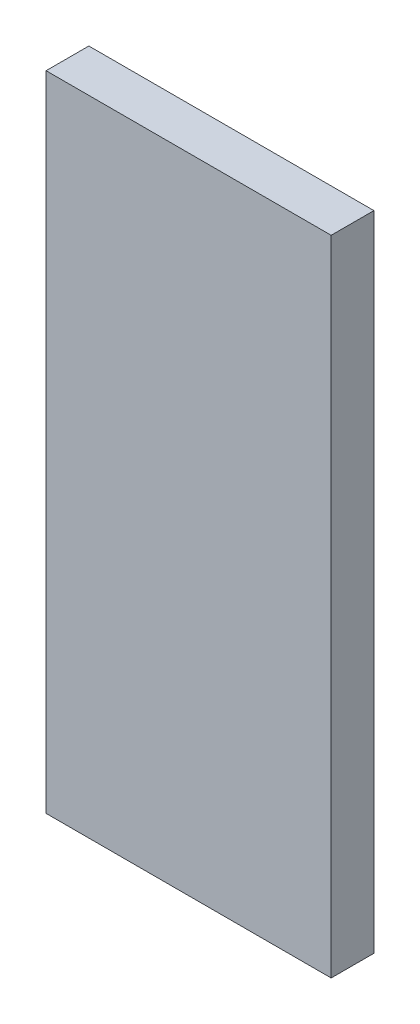
SolidWorks part; units mm, degrees
ref_plane "Alzado" through (0, 0, 0) normal (0, 0, 1) x (1, 0, 0)
ref_plane "Planta" through (0, 0, 0) normal (0, 1, 0) x (1, 0, 0)
ref_plane "Vista lateral" through (0, 0, 0) normal (1, 0, 0) x (0, 0, -1)
sketch "Croquis1" plane through (0, 0, 0) normal (0, 0, 1) x (1, 0, 0)
  line L1 (-40, -90.25) -> (40, -90.25)
  line L2 (-40, -90.25) -> (-40, 90.25)
  line L3 (-40, 90.25) -> (40, 90.25)
  line L4 (40, -90.25) -> (40, 90.25)
  line L5 (-40, -90.25) -> (40, 90.25) construction
  line L6 (-40, 90.25) -> (40, -90.25) construction
  point P0 (0, 0)
  dimension "D1" = 180.5
  dimension "80" = 80
extrude "Saliente-Extruir1" add sketch "Croquis1" along normal blind 12
